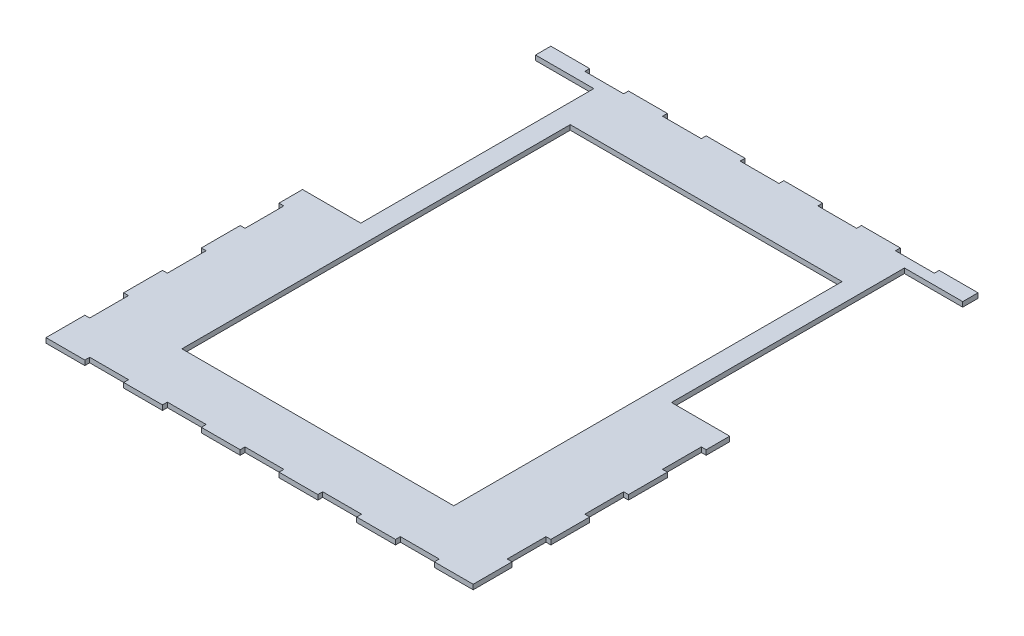
SolidWorks part; units mm, degrees
ref_plane "Front Plane" through (0, 0, 0) normal (0, 0, 1) x (1, 0, 0)
ref_plane "Top Plane" through (0, 0, 0) normal (0, 1, 0) x (1, 0, 0)
ref_plane "Right Plane" through (0, 0, 0) normal (1, 0, 0) x (0, 0, -1)
sketch "Sketch1" plane through (0, 0, 0) normal (0, 1, 0) x (1, 0, 0)
  line L0 (-139.7, 0) -> (0, 0)
  line L1 (0, 0) -> (0, 161.925)
  line L4 (0, 161.925) -> (-12.7, 161.925)
  line L5 (-12.7, 161.925) -> (-12.7, 165.1)
  line L6 (-12.7, 165.1) -> (-38.1, 165.1)
  line L7 (-38.1, 165.1) -> (-38.1, 161.925)
  line L9 (-114.3, 161.925) -> (-114.3, 165.1)
  line L10 (-114.3, 165.1) -> (-139.7, 165.1)
  line L11 (-139.7, 165.1) -> (-139.7, 139.7)
  line L12 (-139.7, 139.7) -> (-136.525, 139.7)
  line L13 (-136.525, 139.7) -> (-136.525, 114.3)
  line L14 (-136.525, 114.3) -> (-139.7, 114.3)
  line L15 (-139.7, 114.3) -> (-139.7, 88.9)
  line L16 (-139.7, 88.9) -> (-136.525, 88.9)
  line L17 (-136.525, 88.9) -> (-136.525, 63.5)
  line L18 (-136.525, 63.5) -> (-139.7, 63.5)
  line L19 (-139.7, 63.5) -> (-139.7, 38.1)
  line L20 (-139.7, 38.1) -> (-136.525, 38.1)
  line L21 (-136.525, 38.1) -> (-136.525, 12.7)
  line L22 (-136.525, 12.7) -> (-139.7, 12.7)
  line L23 (-139.7, 12.7) -> (-139.7, 0)
  line L24 (-114.3, 161.925) -> (-88.9, 161.925)
  line L25 (-88.9, 161.925) -> (-88.9, 165.1)
  line L26 (-88.9, 165.1) -> (-63.5, 165.1)
  line L27 (-63.5, 165.1) -> (-63.5, 161.925)
  line L28 (-63.5, 161.925) -> (-38.1, 161.925)
  dimension "D1" = 25.4
  dimension "D2" = 12.7
  dimension "D3" = 25.4
  dimension "D4" = 12.7
extrude "Boss-Extrude1" add sketch "Sketch1" along normal blind 3.175
mirror "Mirror1" about plane through (-139.7, 3.175, 0) normal (0, 0, -1) of bodies 101
sketch "Sketch4" plane through (0, 3.175, 0) normal (0, 1, 0) x (1, 0, 0)
  line L1 (-139.7, 155.1) -> (-101.6, 155.1)
  line L2 (-139.7, 155.1) -> (-139.7, 2.7)
  line L3 (-139.7, 2.7) -> (-101.6, 2.7)
  line L4 (-101.6, 155.1) -> (-101.6, 2.7)
  line L7 (-139.7, 114.3) -> (-139.7, 88.9) construction
  line L8 (-114.3, 165.1) -> (-139.7, 165.1) construction
  point P4 (-73.7891, 124.7053)
  point P5 (-115.7508, 127.1031)
  point P6 (-123.7435, 121.9078)
  dimension "D1" = 10
  dimension "D2" = 152.4
  dimension "D3" = 38.1
extrude "Cut-Extrude2" cut sketch "Sketch4" against normal through all both and the other way through all
mirror "Mirror2" about plane through (0, 3.175, 0) normal (-1, 0, 0) of bodies 106
sketch "Sketch2" plane through (0, 3.175, 0) normal (0, 1, 0) x (1, 0, 0)
  line L1 (-88.9, -127) -> (88.9, -127)
  line L2 (-88.9, -127) -> (-88.9, 127)
  line L3 (-88.9, 127) -> (88.9, 127)
  line L4 (88.9, -127) -> (88.9, 127)
  line L5 (-88.9, -127) -> (88.9, 127) construction
  line L6 (-88.9, 127) -> (88.9, -127) construction
  circle A0 centre (-88.9, 139.7) radius 3.5
  circle A1 centre (88.9, 139.7) radius 3.5
  circle A2 centre (88.9, -139.7) radius 3.5
  circle A3 centre (-88.9, -139.7) radius 3.5
  point P0 (0, 0)
  point P14 (0, 0)
  point P15 (0, 0)
  point P16 (0, 0)
  point P17 (-102.3144, 141.0837)
  point P18 (0, 0)
  dimension "D3" = 7
  dimension "D1" = 177.8
  dimension "D2" = 254
  dimension "D4" = 12.7
  dimension "D5" = 12.7
extrude "Cut-Extrude1" cut sketch "Sketch2" against normal through all both and the other way through all
